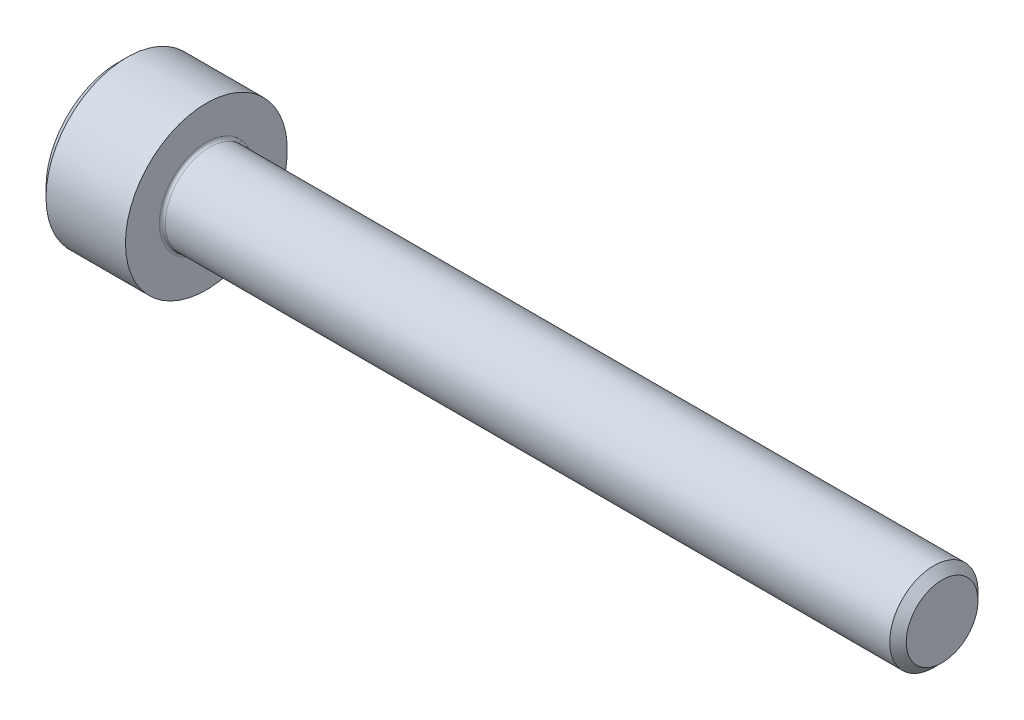
SolidWorks part; units mm, degrees
revolve "Base-Revolve" add sketch "BodySke"
sketch "BodySke" plane through (0, 0, 0) normal (0, 0, 1) x (1, 0, 0)
  line L0 (0, 0) -> (0, 2.45)
  line L1 (0.3, 2.75) -> (3, 2.75)
  line L2 (3, 2.75) -> (3, 1.5)
  line L3 (3, 1.5) -> (27.7195, 1.5)
  line L4 (28, 1.2195) -> (28, 0)
  line L5 (28, 0) -> (0, 0)
  line L6 (-31.75, 0) -> (127, 0) construction
  line L7 (0, 2.45) -> (0.3, 2.75)
  line L8 (28, 1.2195) -> (27.7195, 1.5)
  line L9 (0, -2.45) -> (0.3, -2.75) construction
  line L10 (28, -1.2195) -> (27.7195, -1.5) construction
  line L11 (3.5, 9.525) -> (3.5, 3.175) construction
  line L12 (3, 9.525) -> (3, 3.175) construction
  line L13 (-22, 9.525) -> (-22, 3.175) construction
  dimension "Diameter" = 3
  dimension "Head_ht" = 3
  dimension "Length" = 25
  dimension "Body_ch_ang" = 45
  dimension "Head_dia" = 5.5
  dimension "Head_ch_ang" = 45
  dimension "Minor_dia" = 2.439
  dimension "Advance" = 0.5
  dimension "Thread_nom" = 25
  dimension "Thread_length" = 50
  dimension "Head_ch_ht" = 0.3
cosmetic thread "ThreadCosmetic" [suppressed]
fillet "Fillet1" radius 0.1 1 edges at (3, 0, 1.5)
ref_plane "Plane1" through (0, 0, 0) normal (0, 0, 1) x (1, 0, 0)
ref_plane "Plane2" through (0, 0, 0) normal (0, 1, 0) x (1, 0, 0)
ref_plane "Plane3" through (0, 0, 0) normal (1, 0, 0) x (0, 0, -1)
sketch "Sketch2" plane through (0, 0, 0) normal (0, 0, 1) x (1, 0, 0)
  line L0 (0, 1.28) -> (1.3, 1.28)
  line L1 (1.3, 1.28) -> (2.039, 0)
  line L2 (-31.75, 0) -> (127, 0) construction
  line L3 (2.039, 0) -> (0, 0)
  line L4 (0, 0) -> (0, 1.28)
  line L5 (0, 2.45) -> (0, -2.45) construction
  line L6 (0, 0) -> (47.625, 0) construction
  line L7 (3, -2.75) -> (3, 2.75) construction
  dimension "D1" = 1.28
  dimension "D2" = 60
revolve "Hex-PreBroach" cut sketch "Sketch2" angle 360 about L6
sketch "Sketch3" plane through (0, 0, 0) normal (-1, 0, 0) x (0, 0.5, 0.866)
  line L0 (0.739, 1.28) -> (-0.739, 1.28)
  line L1 (-0.739, 1.28) -> (-1.478, 0)
  line L2 (0.739, 1.28) -> (1.478, 0)
  line L3 (0.739, -1.28) -> (1.478, 0)
  line L4 (0.739, -1.28) -> (-0.739, -1.28)
  line L5 (-0.739, -1.28) -> (-1.478, 0)
  dimension "D1" = 1.28
  dimension "D2" = 1.28
  dimension "Hex_size" = 2.56
extrude "Hex" cut sketch "Sketch3" against normal blind 1.3
sketch "Sketch4" plane through (0, 0, 0) normal (-1, 0, 0) x (0, 0, 1)
  line L0 (0, 0) -> (1.4605, 0)
  line L1 (0, 0) -> (6.1484, 3.5498) construction
  line L2 (0, 0) -> (0.7302, 1.2648)
  line L3 (1.2009, 0.3267) -> (1.3933, 0.4378)
  line L4 (0.8834, 0.8767) -> (1.0758, 0.9877)
  arc A0 (1.2009, 0.3267) -> (0.8834, 0.8767) centre (0, 0) ccw
  arc A1 (1.4605, 0) -> (1.3933, 0.4378) centre (0, 0) ccw
  arc A2 (0.7302, 1.2648) -> (1.0758, 0.9877) centre (0, 0) cw
  dimension "D1" = 30
  dimension "D2" = 60
  dimension "Spline_p_dim" = 0.635
  dimension "D3" = 0.3175
extrude "Spline" [suppressed] cut sketch "Sketch4" against normal blind 1.3
pattern_circular "CirPattern1" [suppressed] count 6 every 60
sketch "Sketch5" plane through (0, 0, 0) normal (0, 0, 1) x (1, 0, 0)
  line L0 (-31.75, 0) -> (127, 0) construction
  line L2 (0, 2.45) -> (0, -2.45) construction
  circle A0 centre (1.2, 0) radius 0.475
  dimension "Drilled_hole_dia" = 0.95
  dimension "Drilled_hole_loc" = 1.2
extrude "Hole" [suppressed] cut sketch "Sketch5" against normal through all and the other way through all
pattern_circular "Drilled-4" [suppressed] count 2 every 60
pattern_circular "Drilled-6" [suppressed] count 3 every 60
sketch "ThdSchSke" plane through (0, 0, 0) normal (0, 0, 1) x (1, 0, 0)
  line L0 (3.5, -1.2195) -> (3.3036, -1.5)
  line L1 (3.5, -1.2195) -> (3.6964, -1.5)
  line L2 (3.6964, -1.5) -> (3.6964, -1.875)
  line L3 (-3.175, 0) -> (5.1513, 0) construction
  line L5 (3.6964, -1.875) -> (3.3036, -1.875)
  line L6 (3.3036, -1.875) -> (3.3036, -1.5)
  line L7 (0, 2.45) -> (0, -2.45) construction
  dimension "Thread_minor" = 2.439
  dimension "Diameter" = 3
  dimension "Start" = 3.5
revolve "ThreadSchematic" [suppressed] cut sketch "ThdSchSke" angle 360 about L3
pattern_linear "ThdSchPat" [suppressed]
equation "\"D2@Sketch3\" = \"Hex_size@Sketch3\" / 2"
equation "\"D1@Sketch3\" = \"Hex_size@Sketch3\" / 2"
equation "\"D1@Sketch2\" = \"Hex_size@Sketch3\" / 2"
equation "\"D3@Sketch4\" = \"Spline_p_dim@Sketch4\" / 2"
equation "\"Thread_minor@ThreadCosmetic\"  =  \"Minor_dia@BodySke\""
equation "\"D2@CirPattern1\" = 360 / \"Num_teeth@CirPattern1\""
equation "\"Wall_thickness@Sketch2\" = \"Head_ht@BodySke\" - \"Key_eng@Hex\""
equation "\"Thread_length@ThreadCosmetic\" = ((sgn( (\"Length@BodySke\" - \"Advance@BodySke\" ) - \"Thread_nom@BodySke\" )-1)*( (\"Length@BodySke\" - \"Advance@BodySke\" ) - \"Thread_nom@BodySke\" ))/-2+ \"Thread_nom@BodySke\""
equation "\"Thread_minor@ThdSchSke\" = \"Minor_dia@BodySke\""
equation "\"Diameter@ThdSchSke\" = \"Diameter@BodySke\""
equation "\"Overcut@ThdSchSke\" = \"Diameter@BodySke\" * 1.25"
equation "\"Start@ThdSchSke\" = \"Head_ht@BodySke\" + \"Length@BodySke\" - \"Thread_length@ThreadCosmetic\"  '---Non-countersunk---"
equation "\"Num_threads@ThdSchPat\" = int( \"Thread_length@ThreadCosmetic\" / \"Advance@BodySke\" + 0.999 )  + 1"
equation "\"Advance@ThdSchPat\" = \"Thread_length@ThreadCosmetic\" /  (\"Num_threads@ThdSchPat\" - 1) 'relax it"
equation "\"Num_threads@ThdSchPat\" = \"Num_threads@ThdSchPat\" - sgn( \"Num_threads@ThdSchPat\" - 1) '---chamfered tips only---"
